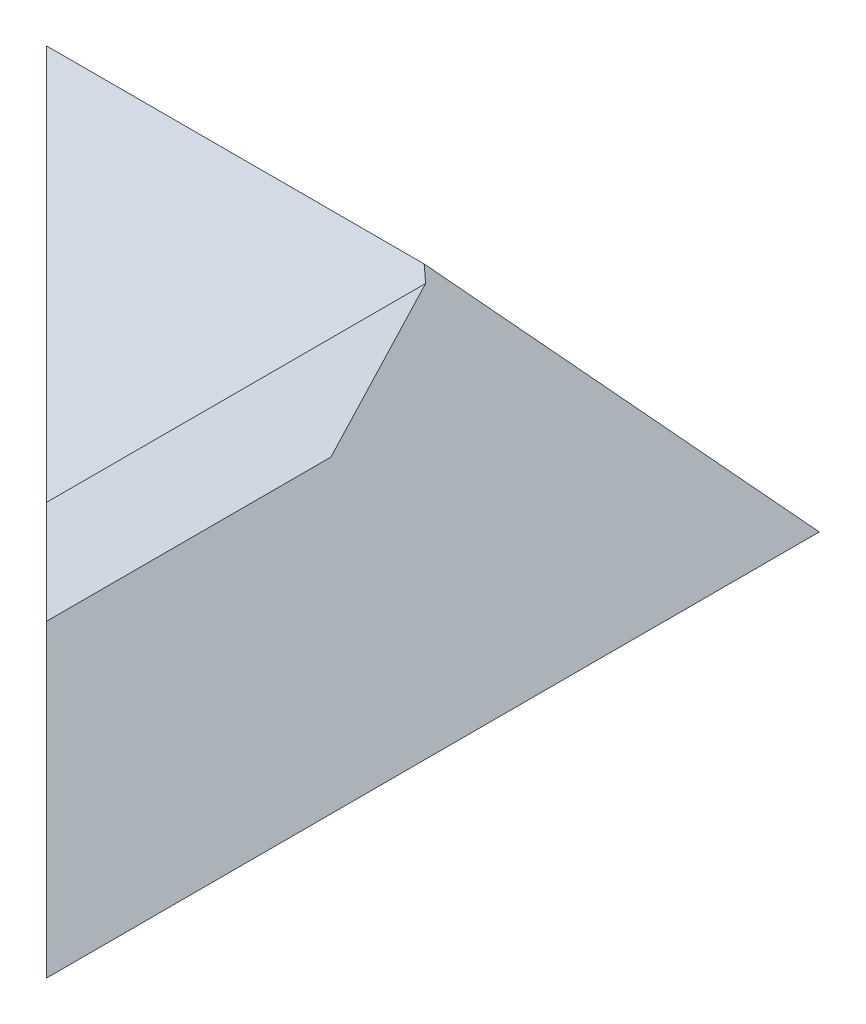
SolidWorks part; units mm, degrees
ref_plane "Front" through (0, 0, 0) normal (0, 0, 1) x (1, 0, 0)
ref_plane "Top" through (0, 0, 0) normal (0, 1, 0) x (1, 0, 0)
ref_plane "Right" through (0, 0, 0) normal (1, 0, 0) x (0, 0, -1)
sketch "Sketch2" plane through (0, 0, 0) normal (1, 0, 0) x (0, 0, -1)
  line L0 (0, 0) -> (35, 41.7114)
  line L1 (35, 41.7114) -> (70, 0)
  line L2 (70, 0) -> (0, 0)
  dimension "D1" = 50
  dimension "D2" = 50
  dimension "D3" = 70
extrude "SurfacesAB" add sketch "Sketch2" along normal blind 150
sketch "Sketch3" plane through (0, 0, 0) normal (0, 0, 1) x (1, 0, 0)
  line L0 (150, 0) -> (120, 30)
  line L1 (120, 30) -> (90, 0)
  line L2 (150, 0) -> (0, 0) construction
  line L3 (90, 0) -> (150, 0)
  dimension "D1" = 45
  dimension "D2" = 45
  dimension "D3" = 60
extrude "SurfacesCD" add sketch "Sketch3" along normal blind 80 and the other way blind 70
sketch "Sketch6" plane through (0, 0, 0) normal (0, 1, 0) x (1, 0, 0)
  line L0 (0, 70) -> (150, -80)
  line L1 (150, -80) -> (0, -80)
  line L2 (0, -80) -> (0, 70)
extrude "Cut-Extrude3" cut sketch "Sketch6" along normal through all
ref_plane "Plane5" through (150, 0, 80) normal (-0.7071, 0, -0.7071) x (-0.7071, 0, 0.7071)
sketch "Sketch13" plane through (150, 0, 80) normal (-0.7071, 0, -0.7071) x (-0.7071, 0, 0.7071)
  line L0 (0, 0) -> (-14.1421, 0)
  line L1 (-14.1421, 0) -> (-79.7997, 50.4887)
  line L2 (0, 0) -> (-80.1048, 61.5982)
  line L3 (-80.1048, 61.5982) -> (-79.7997, 50.4887)
extrude "SurfaceE" add sketch "Sketch13" along normal blind 130
sketch "Sketch10" plane through (0, 0, 0) normal (0, 0, 1) x (1, 0, 0)
  line L0 (150, 0) -> (83.4321, 66.5679)
  line L2 (150, 66.5679) -> (83.4321, 66.5679)
  line L3 (150, 0) -> (213.2358, 0)
  line L4 (213.2358, 0) -> (213.2358, 66.5679)
  line L5 (213.2358, 66.5679) -> (150, 66.5679)
sketch "Sketch4" plane through (150, 0, 0) normal (1, 0, 0) x (0, 0, -1)
  line L0 (70, 0) -> (18.6861, 61.1535)
  line L1 (18.6861, 61.1535) -> (70, 61.1535)
  line L2 (70, 0) -> (70, 61.1535)
extrude "Cut-Extrude9" cut sketch "Sketch10" against normal through all and the other way through all
extrude "Cut-Extrude10" cut sketch "Sketch4" against normal blind 150
ref_plane "AD Dihedral Angle Plane" through (129.1443, 20.8557, -52.5) normal (0.6081, -0.6081, -0.5103) x (0.7938, 0.4658, 0.3909)
